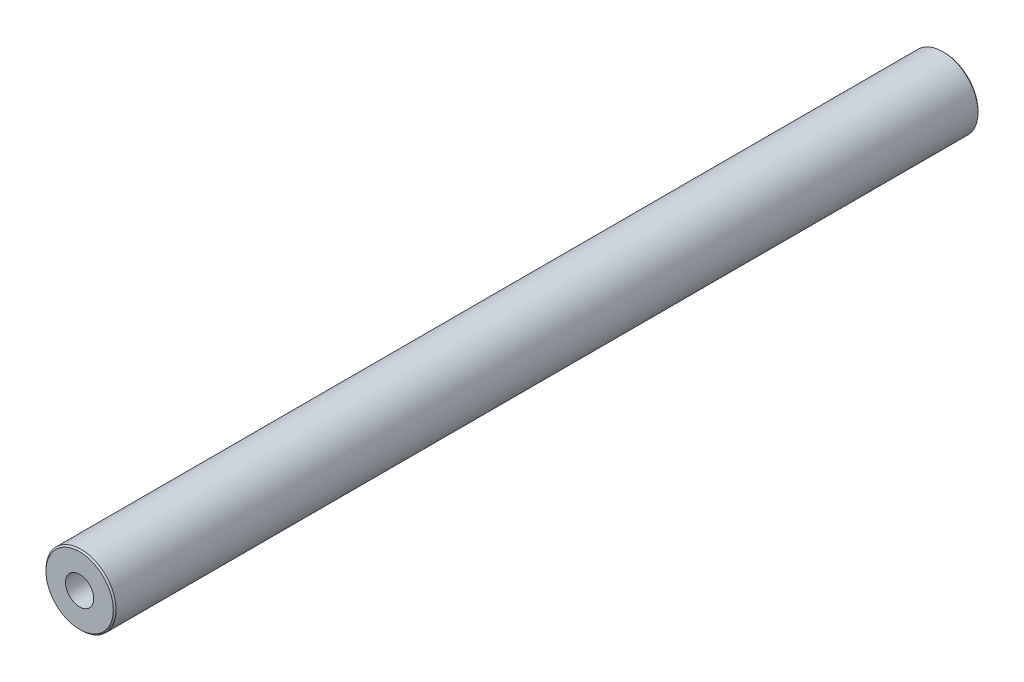
SolidWorks part; units mm, degrees
material "6061-T6 (SS)"
ref_plane "Front" through (0, 0, 0) normal (0, 0, 1) x (1, 0, 0)
ref_plane "Top" through (0, 0, 0) normal (0, 1, 0) x (1, 0, 0)
ref_plane "Right" through (0, 0, 0) normal (1, 0, 0) x (0, 0, -1)
sketch "Sketch1" plane through (0, 0, 0) normal (0, 0, 1) x (1, 0, 0)
  circle A0 centre (0, 0) radius 6.35
  dimension "D2" = 12.7
extrude "Boss-Extrude1" add sketch "Sketch1" along normal mid plane 156.5148
hole_wizard "1/4-20 Tapped Hole1" positions "Sketch3" profile "Sketch2" tap size "1/4-20" standard "Ansi Inch"
sketch "Sketch3" plane through (0, 0, 78.2574) normal (0, 0, 1) x (1, 0, 0)
  circle A0 centre (0, 0) radius 6.35 construction
  point P0 (0, 0)
sketch "Sketch2" plane through (0, 0, 78.2574) normal (1, 0, 0) x (0, -1, 0)
  line L0 (0, 0) -> (0, 41.5338)
  line L1 (0, 41.5338) -> (2.5527, 40)
  line L2 (2.5527, 40) -> (2.5527, 0)
  line L5 (2.5527, 0) -> (0, 0)
  line L10 (0, 41.5338) -> (-2.5527, 40) construction
  line L11 (0, -6.35) -> (0, 107.95) construction
  dimension "Tap Drill Dia." = 5.1054
  dimension "Tap Drill Depth" = 40
  dimension "Drill Angle" = 118
cosmetic thread "Hole Thread2" parameters "D1"=12.7, "D2"=6.35
hole_wizard "1/4-20 Tapped Hole2" positions "Sketch5" profile "Sketch4" tap size "1/4-20" standard "Ansi Inch"
sketch "Sketch5" plane through (0, 0, -78.2574) normal (0, 0, -1) x (-1, 0, 0)
  circle A0 centre (0, 0) radius 6.35 construction
  point P0 (0, 0)
sketch "Sketch4" plane through (0, 0, -78.2574) normal (1, 0, 0) x (0, 1, 0)
  line L0 (0, 0) -> (0, 41.5338)
  line L1 (0, 41.5338) -> (2.5527, 40)
  line L2 (2.5527, 40) -> (2.5527, 0)
  line L5 (2.5527, 0) -> (0, 0)
  line L10 (0, 41.5338) -> (-2.5527, 40) construction
  line L11 (0, -6.35) -> (0, 107.95) construction
  dimension "Tap Drill Dia." = 5.1054
  dimension "Tap Drill Depth" = 40
  dimension "Drill Angle" = 118
cosmetic thread "Hole Thread3" parameters "D1"=12.7, "D2"=6.35
chamfer "Chamfer1" distance 0.254 angle 45 2 edges at (6.35, 0, -78.2574) (6.35, 0, 78.2574)
